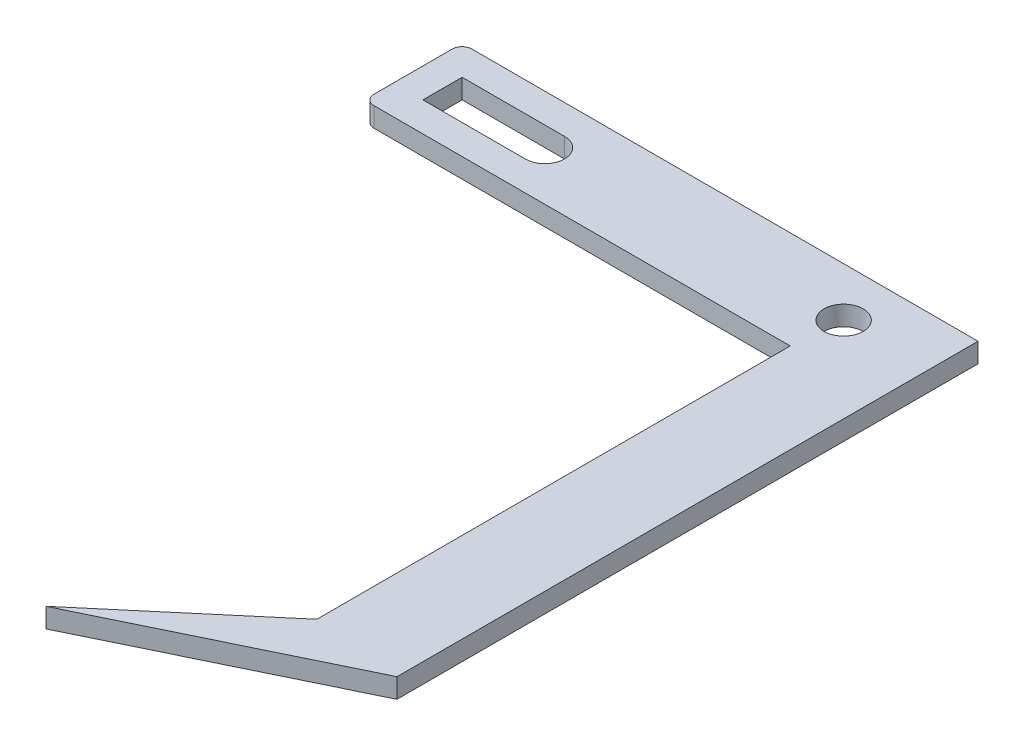
SolidWorks part; units mm, degrees
ref_plane "Front Plane" through (0, 0, 0) normal (0, 0, 1) x (1, 0, 0)
ref_plane "Top Plane" through (0, 0, 0) normal (0, 1, 0) x (1, 0, 0)
ref_plane "Right Plane" through (0, 0, 0) normal (1, 0, 0) x (0, 0, -1)
sketch "Sketch1" plane through (0, 0, 0) normal (0, 1, 0) x (1, 0, 0)
  line L0 (0, 48.4129) -> (0, 37.692)
  line L1 (1, 36.692) -> (31.48, 36.692)
  line L2 (15, 41.7006) -> (15, -27.2696) construction
  line L3 (31.48, 36.692) -> (43.0365, 36.692)
  line L4 (43.0365, 36.692) -> (43.0365, -13.308)
  line L5 (54.2008, -12.6029) -> (54.2008, 10.2676)
  line L6 (1, 49.4129) -> (41.48, 49.4129)
  line L7 (41.48, 49.4129) -> (54.2008, 49.4129)
  line L9 (15, 43.7006) -> (4.5495, 43.7006)
  line L10 (4.5495, 43.7006) -> (4.5495, 39.7006)
  line L11 (4.5495, 39.7006) -> (15, 39.7006)
  line L13 (30.0717, -24.2882) -> (36, -19.2674)
  line L15 (54.2008, 49.4129) -> (54.2008, 10.2676)
  line L17 (38.3103, -17.3107) -> (43.0365, -13.308)
  line L19 (36, -19.2674) -> (34.2536, -17.3107)
  line L20 (30.0717, -24.2882) -> (54.2008, -12.6029)
  line L21 (34.2536, -17.3107) -> (38.3103, -17.3107)
  arc A4 (1, 36.692) -> (0, 37.692) centre (1, 37.692) cw
  arc A5 (1, 49.4129) -> (0, 48.4129) centre (1, 48.4129) ccw
  arc A6 (15, 39.7006) -> (15, 43.7006) centre (15, 41.7006) ccw
  circle A7 centre (45.48, 41.7006) radius 2
  point P9 (36, 36.692)
  point P18 (0, 36.692)
  point P21 (0, 49.4129)
  dimension "D5" = 40.48
  dimension "D7" = 1
  dimension "D8" = 15
  dimension "D10" = 4
  dimension "D11" = 30.48
extrude "Boss-Extrude2" add sketch "Sketch1" along normal blind 2
sketch "Sketch2" plane through (0, 2, 0) normal (0, 1, 0) x (1, 0, 0)
ref_plane "Plane1" through (1, 2, -36.692) normal (1, 0, 0) x (0, 0, -1)
sketch "Sketch6" plane through (0, 2, 0) normal (0, 1, 0) x (1, 0, 0)
  line L0 (36, -19.2674) -> (38.3103, -17.3107)
  line L2 (38.3103, -17.3107) -> (34.2536, -17.3107)
  line L3 (34.2536, -17.3107) -> (36, -19.2674)
extrude "Cut-Extrude2" cut sketch "Sketch6" against normal blind 9
sketch "Sketch8" plane through (0, 2, 0) normal (0, 1, 0) x (1, 0, 0)
  line L0 (43.0365, 36.692) -> (45.0365, 36.692)
  line L1 (1, 36.692) -> (43.0365, 36.692) construction
  line L2 (45.0365, 36.692) -> (45.0365, -11.1155)
  line L3 (43.0365, -13.308) -> (45.0365, -11.6141)
  line L4 (43.0365, -13.308) -> (30.0717, -24.2882) construction
  line L5 (45.0365, -11.1155) -> (45.0365, -11.6141)
  line L6 (43.0365, -13.308) -> (43.0365, 36.692)
extrude "Cut-Extrude3" cut sketch "Sketch8" against normal blind 9
sketch "Sketch9" plane through (0, 2, 0) normal (0, 1, 0) x (1, 0, 0)
  line L0 (45.0365, 36.692) -> (54.2008, 36.692)
  line L1 (54.2008, -12.6029) -> (54.2008, 49.4129) construction
  line L2 (54.2008, 36.692) -> (54.2008, 46.692)
  line L3 (54.2008, 46.692) -> (0, 46.692)
  line L4 (0, 48.4129) -> (0, 37.692) construction
  line L5 (0, 46.692) -> (0, 36.692)
  line L6 (45.0365, 36.692) -> (0, 36.692)
  line L7 (54.2008, 46.692) -> (54.2008, 49.4129)
  line L8 (54.2008, 49.4129) -> (0, 49.4129)
  line L9 (0, 46.692) -> (0, 49.4129)
  line M10 (54.2008, -12.6029) -> (54.2008, 49.4129)
  line M11 (54.2008, 49.4129) -> (1, 49.4129)
  arc M12 (1, 49.4129) -> (0, 48.4129) centre (1, 48.4129) ccw
  line M13 (0, 48.4129) -> (0, 37.692)
extrude "Cut-Extrude4" cut sketch "Sketch9" against normal blind 10 contours L3 M10 M11 M12 M13
ref_plane "Plane2" through (0, 2, -46.692) normal (-1, 0, 0) x (0, 0, 1)
sketch "Sketch11" plane through (0, 2, 0) normal (0, 1, 0) x (1, 0, 0)
  line L0 (0, 46.692) -> (1, 46.692)
  line L1 (54.2008, 46.692) -> (0, 46.692) construction
  line L2 (1, 46.692) -> (1, 45.692)
  line L3 (0, 46.692) -> (0, 45.692)
  circle A0 centre (1, 45.692) radius 1
  line M7 (54.2008, 46.692) -> (0, 46.692)
  line M8 (0, 46.692) -> (0, 37.692)
extrude "Cut-Extrude5" cut sketch "Sketch11" against normal blind 10 contours A0 M7 M8
sketch "Sketch12" plane through (0, 2, 0) normal (0, 1, 0) x (1, 0, 0)
  line L0 (4.5495, 41.7006) -> (1.5495, 41.7006)
  line L1 (4.5495, 43.7006) -> (4.5495, 39.7006) construction
  line L2 (1.5495, 41.7006) -> (1.5495, 46.692)
  line L3 (54.2008, 46.692) -> (1, 46.692) construction
  line L4 (1.5495, 46.692) -> (0, 46.692)
  line L5 (0, 46.692) -> (0, 36.6271)
  line L6 (0, 36.6271) -> (1.5495, 36.6271)
  line L7 (1.5495, 36.6271) -> (1.5495, 41.7006)
  line M6 (54.2008, 46.692) -> (1, 46.692)
  arc M7 (1, 46.692) -> (0, 45.692) centre (1, 45.692) ccw
  line M8 (0, 45.692) -> (0, 37.692)
  arc M9 (0, 37.692) -> (1, 36.692) centre (1, 37.692) ccw
  line M10 (1, 36.692) -> (45.0365, 36.692)
extrude "Cut-Extrude6" cut sketch "Sketch12" against normal blind 10 contours L7 L2 M10 M6 M7 M8 M9
sketch "Sketch13" plane through (0, 2, 0) normal (0, 1, 0) x (1, 0, 0)
  line L0 (1.5495, 46.692) -> (2.5495, 46.692)
  line L1 (54.2008, 46.692) -> (1.5495, 46.692) construction
  line L2 (2.5495, 46.692) -> (2.5495, 45.692)
  line L3 (1.5495, 36.692) -> (2.5495, 36.692)
  line L4 (1.5495, 36.692) -> (45.0365, 36.692) construction
  line L5 (2.5495, 36.692) -> (2.5495, 37.692)
  line L6 (1.5495, 36.692) -> (1.5495, 37.692)
  line L7 (1.5495, 45.692) -> (1.5495, 46.692)
  circle A0 centre (2.5495, 45.692) radius 1
  circle A1 centre (2.5495, 37.692) radius 1
  line M1 (1.5495, 46.692) -> (1.5495, 36.692)
  line M2 (1.5495, 36.692) -> (45.0365, 36.692)
  line M7 (54.2008, 46.692) -> (1.5495, 46.692)
extrude "Cut-Extrude8" cut sketch "Sketch13" against normal blind 20 contours A1 M1 M2 | A0 M7 M1
